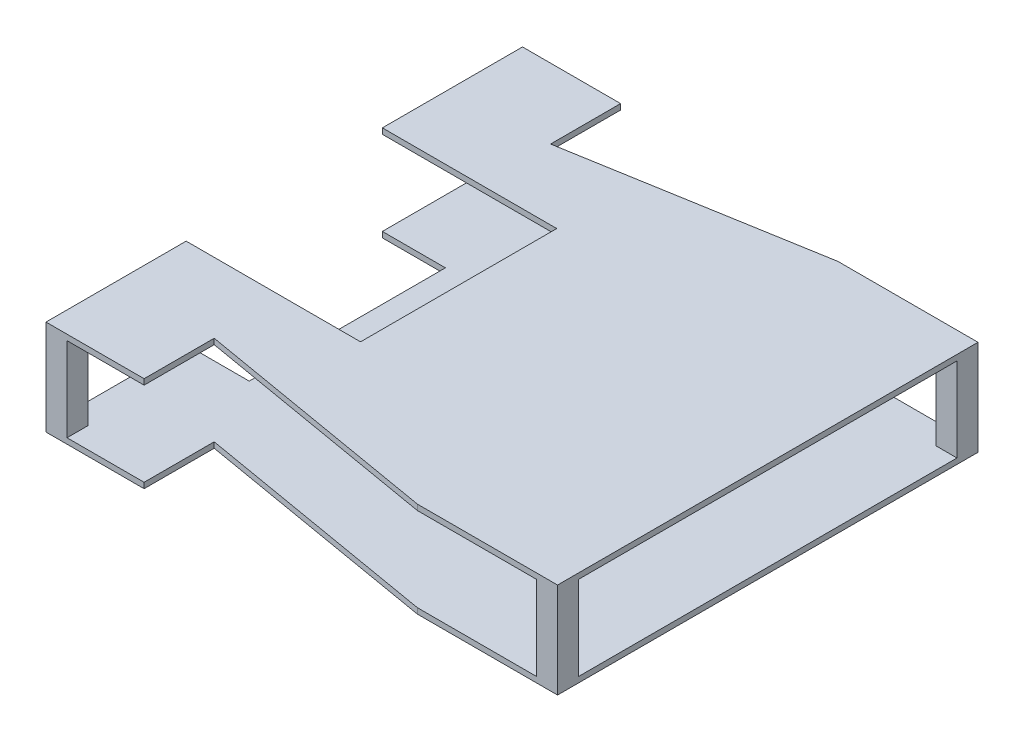
SolidWorks part; units mm, degrees
ref_plane "Front Plane" through (0, 0, 0) normal (0, 0, 1) x (1, 0, 0)
ref_plane "Top Plane" through (0, 0, 0) normal (0, 1, 0) x (1, 0, 0)
ref_plane "Right Plane" through (0, 0, 0) normal (1, 0, 0) x (0, 0, -1)
sketch "Sketch2" plane through (0, 0, 0) normal (0, 1, 0) x (1, 0, 0)
  line L0 (0, 35) -> (0, -35)
  line L3 (12.5, -60) -> (100, -75)
  line L4 (100, -75) -> (150, -75)
  line L5 (150, -75) -> (150, 75)
  line L7 (100.1809, 75) -> (150, 75)
  line L8 (12.6809, 60) -> (100.1809, 75)
  line L9 (12.5, 60) -> (12.6809, 60)
  line L10 (12.6809, 60) -> (12.5, 60)
  line L11 (0, -35) -> (0, 35) construction
  line L12 (-22.5, -35) -> (0, -35)
  line L13 (-22.5, -35) -> (-22.5, -85)
  line L14 (-22.5, -85) -> (12.5, -85)
  line L15 (12.5, -60) -> (12.5, -85)
  line L16 (0, 35) -> (-22.5, 35)
  line L17 (12.5, 60) -> (12.5, 85)
  line L18 (12.5, 85) -> (-22.5, 85)
  line L19 (-22.5, 35) -> (-22.5, 85)
  line L20 (0, 35) -> (0, -35) construction
  line L21 (0, 35) -> (0, -35) construction
  point P5 (0, 0)
  point P18 (0, 0)
  point P26 (0, 0)
  point P27 (0, 0)
  dimension "D1" = 150
  dimension "D3" = 50
  dimension "D4" = 50
  dimension "D6" = 50
  dimension "D7" = 35
  dimension "D8" = 70
  dimension "D10" = 35
extrude "Boss-Extrude1" add sketch "Sketch2" along normal blind 2
sketch "Sketch3" plane through (0, 2, 0) normal (0, 1, 0) x (1, 0, 0)
  line L4 (150, 75) -> (142.5, 75)
  line L5 (150, 75) -> (150, 67.5)
  line L6 (150, 67.5) -> (142.5, 67.5)
  line L7 (142.5, 75) -> (142.5, 67.5)
  line L8 (150, -75) -> (142.5, -75)
  line L9 (150, -75) -> (150, -67.5)
  line L10 (150, -67.5) -> (142.5, -67.5)
  line L11 (142.5, -75) -> (142.5, -67.5)
  line L12 (-22.5, 85) -> (-15, 85)
  line L13 (-22.5, 85) -> (-22.5, 77.5)
  line L14 (-22.5, 77.5) -> (-15, 77.5)
  line L15 (-15, 85) -> (-15, 77.5)
  line L16 (-22.5, -85) -> (-15, -85)
  line L17 (-22.5, -85) -> (-22.5, -77.5)
  line L18 (-22.5, -77.5) -> (-15, -77.5)
  line L19 (-15, -85) -> (-15, -77.5)
  point P20 (0, 0)
  point P21 (-22.5, -85)
  point P23 (0, 0)
  point P24 (-22.5, -85)
  point P25 (-22.5, -85)
  point P26 (0, 0)
  point P27 (-22.5, 85)
  dimension "D1" = 7.5
  dimension "D4" = 7.5
  dimension "D2" = 7.5
  dimension "D3" = 7.5
  dimension "D5" = 7.5
  dimension "D6" = 7.5
  dimension "D7" = 7.5
  dimension "D8" = 7.5
extrude "Boss-Extrude2" add sketch "Sketch3" along normal blind 30
sketch "Sketch5" plane through (0, 32, 0) normal (0, 1, 0) x (1, 0, 0)
  line L0 (150, 75) -> (100, 75)
  line L1 (100, 75) -> (12.5, 60)
  line L2 (-22.5, 65) -> (-22.5, 35)
  line L3 (12.5, -60) -> (100, -75)
  line L4 (100, -75) -> (150, -75)
  line L5 (150, -75) -> (150, 75)
  line L6 (-22.5, 35) -> (39.7178, 35)
  line L7 (39.7178, 35) -> (39.7178, -35)
  line L8 (39.7178, -35) -> (-22.5, -35)
  line L10 (150, 67.5) -> (150, 75) construction
  line L11 (-22.5, -35) -> (-22.5, -85)
  line L14 (-22.5, -85) -> (12.5, -85)
  line L15 (12.5, -85) -> (12.5, -60)
  line L16 (-22.5, 65) -> (-22.5, 85)
  line L17 (-15, 85) -> (-22.5, 85) construction
  line L18 (-22.5, 85) -> (12.5, 85)
  line L19 (12.5, 85) -> (12.5, 60)
  line L20 (-15, -85) -> (12.5, -85) construction
  line L21 (-22.5, -35) -> (0, -35) construction
  line L22 (-22.5, -35) -> (-22.5, -77.5) construction
  line L23 (0, 35) -> (-22.5, 35) construction
  point P15 (0, 0)
  point P27 (0, 0)
  point P29 (0, 0)
  point P31 (0, 0)
  point P33 (0, 0)
  point P37 (0, 0)
  point P39 (0, 0)
  dimension "D1" = 50
  dimension "D2" = 30
extrude "Boss-Extrude3" add sketch "Sketch5" along normal blind 2
